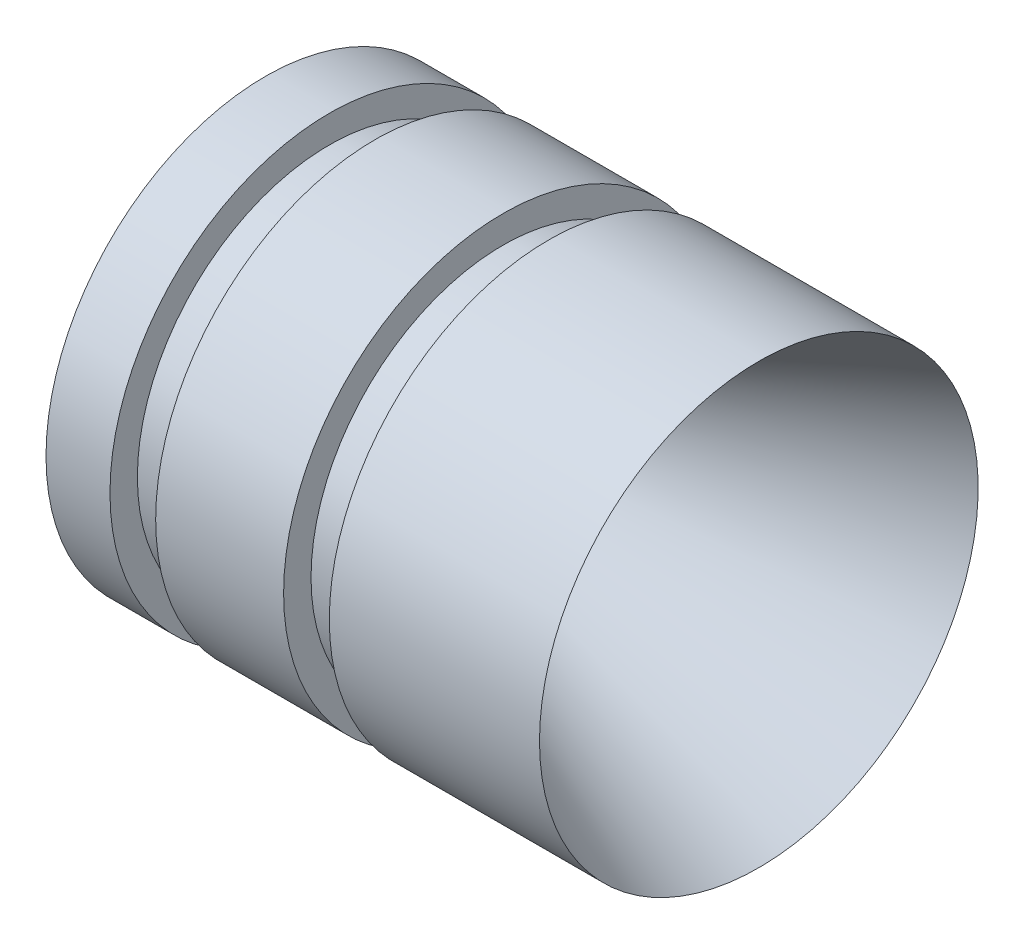
SolidWorks part; units mm, degrees
material "Titanium Ti-8Al-1Mo-1V"
ref_plane "Front Plane" through (0, 0, 0) normal (0, 0, 1) x (1, 0, 0)
ref_plane "Top Plane" through (0, 0, 0) normal (0, 1, 0) x (1, 0, 0)
ref_plane "Right Plane" through (0, 0, 0) normal (1, 0, 0) x (0, 0, -1)
sketch "Sketch1" plane through (0, 0, 0) normal (0, 1, 0) x (1, 0, 0)
  line L0 (-4.5776, -6.012) -> (22.4224, -6.012) construction
  line L1 (-4.5776, 5.988) -> (-1.0776, 5.988)
  line L9 (-4.5776, 5.988) -> (2.4224, -0.762)
  line L12 (2.4224, -0.762) -> (7.4224, -0.762)
  line L14 (-1.0776, 5.988) -> (-1.0776, 4.488)
  line L15 (-1.0776, 4.488) -> (1.4224, 4.488)
  line L16 (7.4224, -0.762) -> (22.4224, 5.988)
  line L17 (1.4224, 4.488) -> (1.4224, 5.988)
  line L19 (1.4224, 5.988) -> (8.4224, 5.988)
  line L20 (8.4224, 5.988) -> (8.4224, 4.488)
  line L21 (8.4224, 4.488) -> (10.9224, 4.488)
  line L22 (10.9224, 4.488) -> (10.9224, 5.988)
  line L23 (10.9224, 5.988) -> (22.4224, 5.988)
  point P4 (4.9224, -6.012)
  dimension "D6" = 7
  dimension "D1" = 27
  dimension "D2" = 3.5
  dimension "D3" = 1.5
  dimension "D4" = 5
  dimension "D5" = 2.5
  dimension "D7" = 2.5
revolve "Revolve1" add sketch "Sketch1" angle 360 about L0
fillet "Fillet1" [suppressed] radius 0.25
fillet "Fillet2" radius 2 2 edges at (2.4224, 0, 11.262) (7.4224, 0, 11.262)
